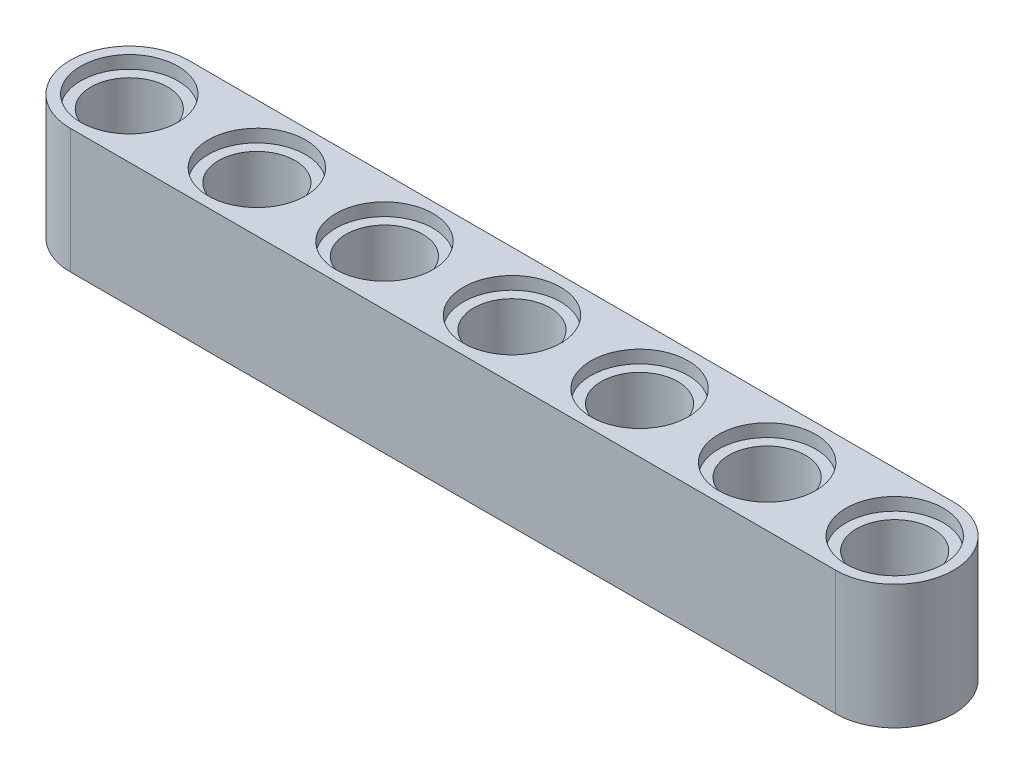
SolidWorks part; units mm, degrees
ref_plane "Front Plane" through (0, 0, 0) normal (0, 0, 1) x (1, 0, 0)
ref_plane "Top Plane" through (0, 0, 0) normal (0, 1, 0) x (1, 0, 0)
ref_plane "Right Plane" through (0, 0, 0) normal (1, 0, 0) x (0, 0, -1)
sketch "Sketch1" plane through (0, 0, 0) normal (0, 1, 0) x (1, 0, 0)
  line L0 (-16, -3.7) -> (32, -3.7)
  line L1 (-16, 3.7) -> (32, 3.7)
  arc A9 (32, 3.7) -> (32, -3.7) centre (32, 0) cw
  arc A10 (-16, 3.7) -> (-16, -3.7) centre (-16, 0) ccw
  point P20 (8, -3.7)
  point P25 (-8, -3.7)
  dimension "D1" = 3.7
  dimension "D5" = 3.7
  dimension "D2" = 48
extrude "Boss-Extrude3" add sketch "Sketch1" along normal blind 7.8 contours A10 L0 A9 L1
sketch "Sketch2" plane through (0, 7.8, 0) normal (0, 1, 0) x (1, 0, 0)
  circle A0 centre (0, 0) radius 2.4
  circle A2 centre (8, 0) radius 2.4
  circle A5 centre (16, 0) radius 2.4
  circle A6 centre (-16, 0) radius 2.4
  circle A9 centre (-8, 0) radius 2.4
  circle A10 centre (24, 0) radius 2.4
  circle A11 centre (32, 0) radius 2.4
  dimension "D1" = 4.8
  dimension "D2" = 8
sketch "Sketch3" plane through (0, 7.8, 0) normal (0, 1, 0) x (1, 0, 0)
  circle A0 centre (0, 0) radius 3.05
  circle A1 centre (8, 0) radius 3.05
  circle A2 centre (16, 0) radius 3.05
  circle A3 centre (-16, 0) radius 3.05
  circle A4 centre (-8, 0) radius 3.05
  circle A5 centre (32, 0) radius 3.05
  circle A6 centre (24, 0) radius 3.05
  dimension "D1" = 6.1
  dimension "D2" = 8
sketch "Sketch4" plane through (0, 0, 0) normal (0, -1, 0) x (1, 0, 0)
  circle A0 centre (0, 0) radius 3.05
  circle A1 centre (8, 0) radius 3.05
  circle A2 centre (16, 0) radius 3.05
  circle A3 centre (-16, 0) radius 3.05
  circle A4 centre (-8, 0) radius 3.05
  circle A5 centre (32, 0) radius 3.05
  circle A6 centre (24, 0) radius 3.05
  dimension "D1" = 6.1
  dimension "D2" = 8
extrude "Cut-Extrude1" cut sketch "Sketch2" against normal blind 7.8
extrude "Cut-Extrude2" cut sketch "Sketch3" against normal blind 0.8
extrude "Cut-Extrude3" cut sketch "Sketch4" against normal blind 0.8
